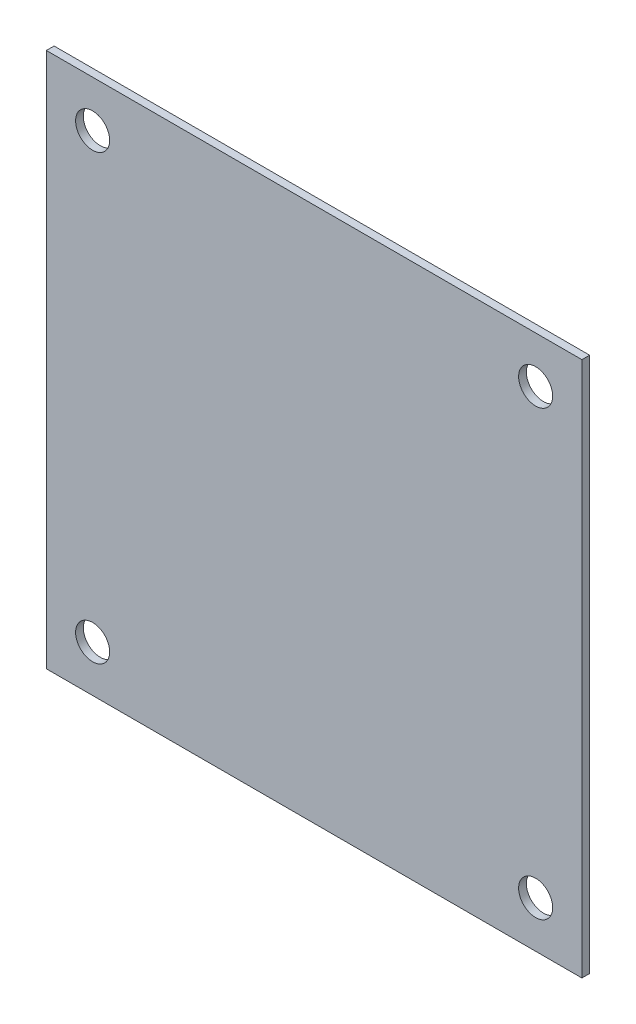
SolidWorks part; units mm, degrees
ref_plane "Front Plane" through (0, 0, 0) normal (0, 0, 1) x (1, 0, 0)
ref_plane "Top Plane" through (0, 0, 0) normal (0, 1, 0) x (1, 0, 0)
ref_plane "Right Plane" through (0, 0, 0) normal (1, 0, 0) x (0, 0, -1)
sketch "Model" plane through (0, 0, 0) normal (0, 0, 1) x (1, 0, 0)
  line L0 (-16.5, -16.5) -> (-16.5, 93.5)
  line L1 (-16.5, 93.5) -> (93.5, 93.5)
  line L2 (93.5, 93.5) -> (93.5, -16.5)
  line L3 (93.5, -16.5) -> (-16.5, -16.5)
  circle A0 centre (84, 84) radius 3.5
  circle A1 centre (-7, 84) radius 3.5
  circle A2 centre (-7, -7) radius 3.5
  circle A3 centre (84, -7) radius 3.5
extrude "Boss-Extrude1" add sketch "Model" along normal blind 1.5875
